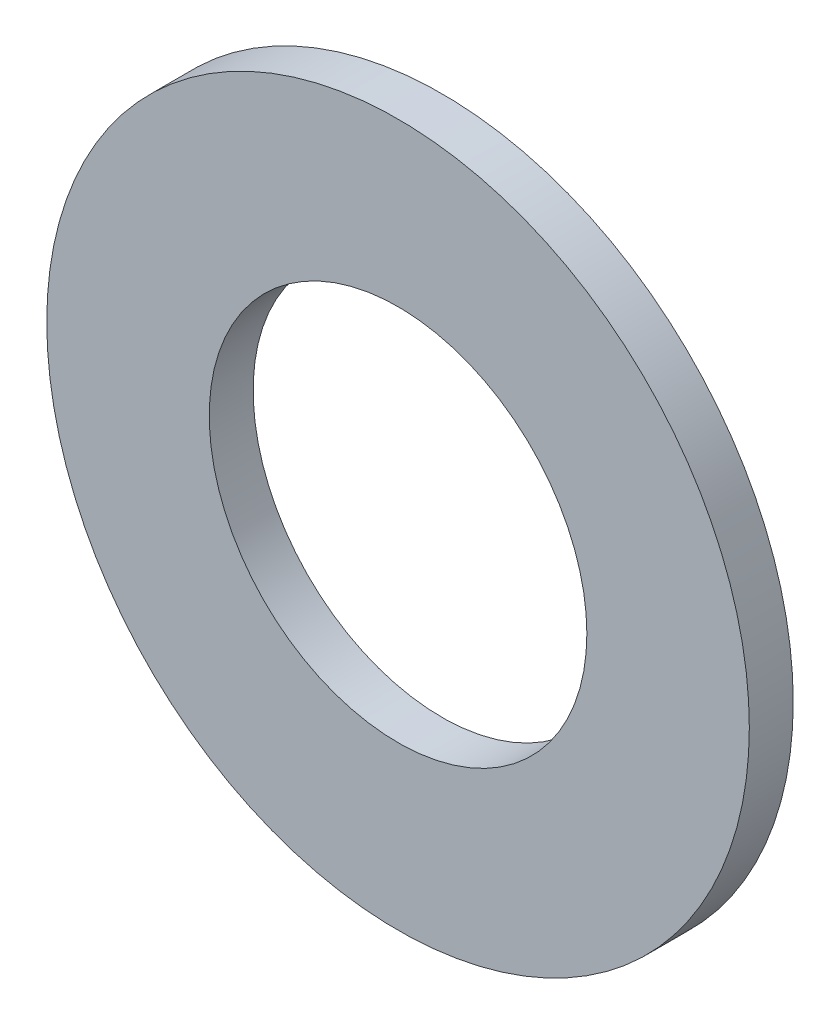
SolidWorks part; units mm, degrees
ref_plane "Спереди" through (0, 0, 0) normal (0, 0, 1) x (1, 0, 0)
ref_plane "Сверху" through (0, 0, 0) normal (0, 1, 0) x (1, 0, 0)
ref_plane "Справа" through (0, 0, 0) normal (1, 0, 0) x (0, 0, -1)
sketch "Эскиз1" plane through (0, 0, 0) normal (0, 0, 1) x (1, 0, 0)
  circle A0 centre (0, 0) radius 4
  circle A1 centre (0, 0) radius 2.15
  dimension "D1" = 8
  dimension "D2" = 4.3
extrude "Бобышка-Вытянуть1" add sketch "Эскиз1" along normal blind 0.5
